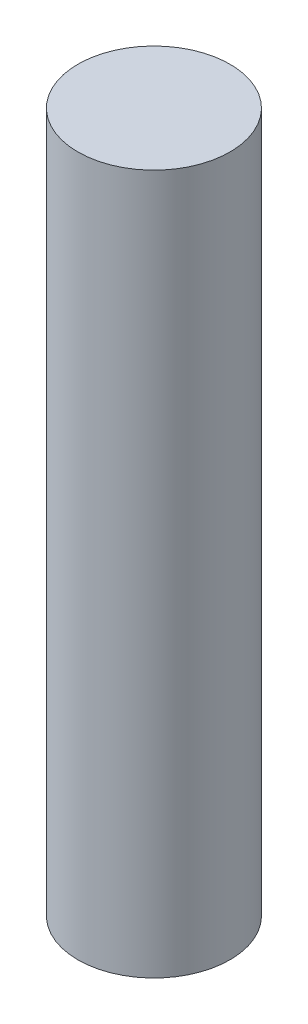
SolidWorks part; units mm, degrees
ref_plane "Front Plane" through (0, 0, 0) normal (0, 0, 1) x (1, 0, 0)
ref_plane "Top Plane" through (0, 0, 0) normal (0, 1, 0) x (1, 0, 0)
ref_plane "Right Plane" through (0, 0, 0) normal (1, 0, 0) x (0, 0, -1)
sketch "Sketch1" plane through (0, 0, 0) normal (0, 1, 0) x (1, 0, 0)
  circle A0 centre (0, 0) radius 0.75
  dimension "D1" = 1.5
extrude "Boss-Extrude1" add sketch "Sketch1" along normal blind 6.9
